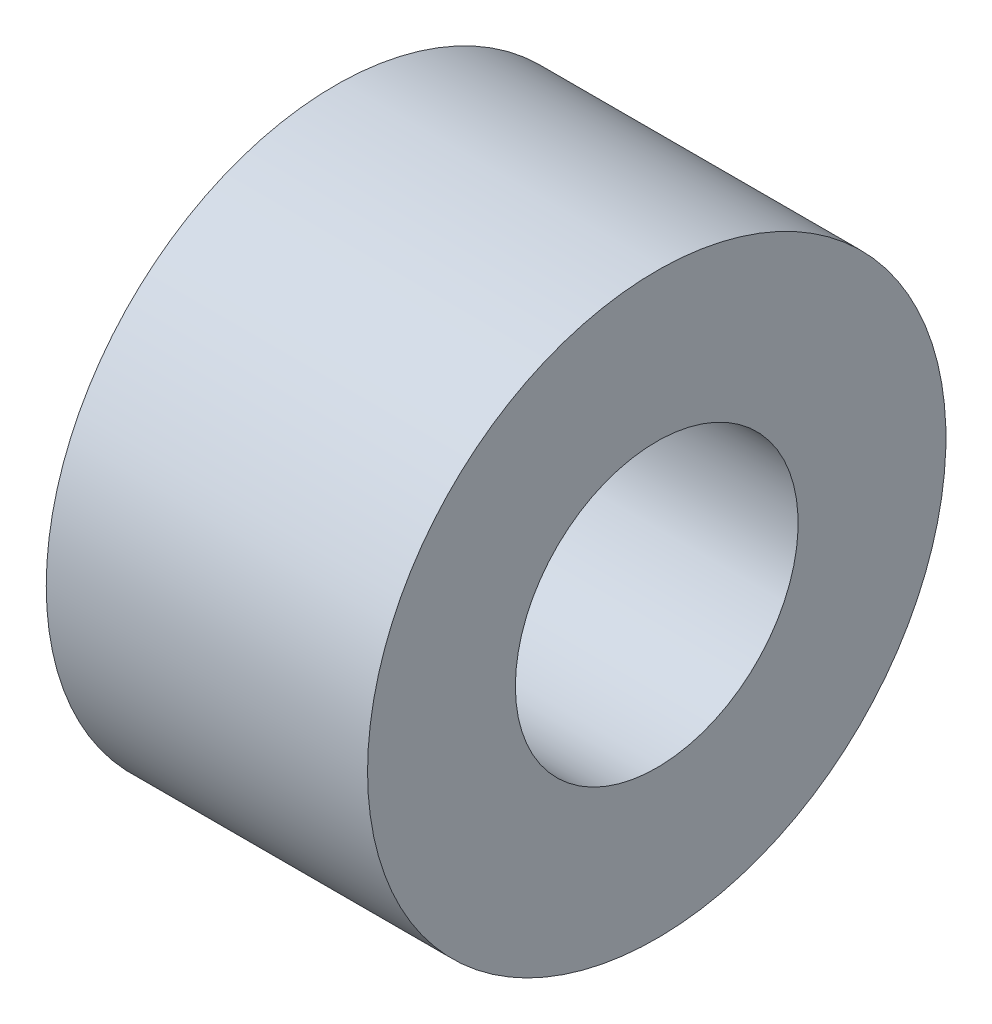
SolidWorks part; units mm, degrees
ref_plane "Front Plane" through (0, 0, 0) normal (0, 0, 1) x (1, 0, 0)
ref_plane "Top Plane" through (0, 0, 0) normal (0, 1, 0) x (1, 0, 0)
ref_plane "Right Plane" through (0, 0, 0) normal (1, 0, 0) x (0, 0, -1)
sketch "Sketch1" plane through (0, 0, 0) normal (0, 0, 1) x (1, 0, 0)
  line L0 (0, 0) -> (7.3225, 0) construction
  line L1 (0, 1.1) -> (2.5, 1.1)
  line L2 (2.5, 1.1) -> (2.5, 2.25)
  line L7 (2.5, 2.25) -> (0, 2.25)
  line L8 (0, 2.25) -> (0, 1.1)
  dimension "D1" = 2.5
  dimension "D2" = 2.2
  dimension "D3" = 4.5
revolve "Revolve1" add sketch "Sketch1" angle 360 about L0
